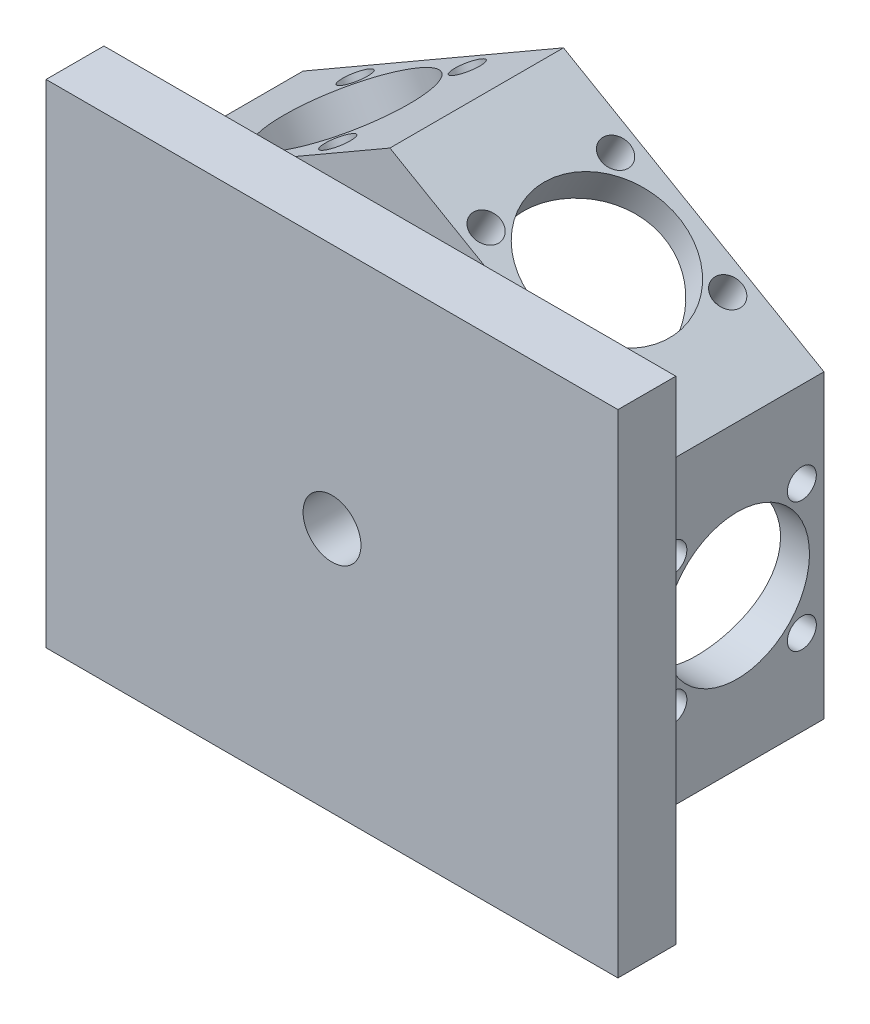
SolidWorks part; units mm, degrees
ref_plane "Front Plane" through (0, 0, 0) normal (0, 0, 1) x (1, 0, 0)
ref_plane "Top Plane" through (0, 0, 0) normal (0, 1, 0) x (1, 0, 0)
ref_plane "Right Plane" through (0, 0, 0) normal (1, 0, 0) x (0, 0, -1)
sketch "Sketch1" plane through (0, 0, 0) normal (0, 0, 1) x (1, 0, 0)
  line L1 (0, -51.9615) -> (45, -25.9808)
  line L2 (45, -25.9808) -> (45, 25.9808)
  line L3 (45, 25.9808) -> (0, 51.9615)
  line L4 (0, 51.9615) -> (-45, 25.9808)
  line L5 (-45, 25.9808) -> (-45, -25.9808)
  line L6 (-45, -25.9808) -> (0, -51.9615)
  circle A0 centre (0, 0) radius 45 construction
  circle A1 centre (0, 0) radius 40
  dimension "D2" = 5
  dimension "D1" = 90
extrude "Boss-Extrude1" add sketch "Sketch1" along normal blind 30
sketch "Sketch2" plane through (22.5, 38.9711, 0) normal (0.5, 0.866, 0) x (0.866, -0.5, 0)
  line L0 (0, 0) -> (0, -30) construction
  line L1 (25.9808, -30) -> (-25.9808, -30) construction
  line L3 (0, -15) -> (-11.1864, -3.8136) construction
  circle A0 centre (0, -15) radius 15.82 construction
  circle A1 centre (-11.1864, -3.8136) radius 2.5
  dimension "D1" = 31.64
  dimension "D2" = 5
extrude "Cut-Extrude1" cut sketch "Sketch2" against normal blind 30
sketch "Sketch3" plane through (22.5, 38.9711, 0) normal (0.5, 0.866, 0) x (0.866, -0.5, 0)
  line L0 (0, 0) -> (0, -30) construction
  line L1 (25.9808, -30) -> (-25.9808, -30) construction
  circle A0 centre (0, -15) radius 12.5
  dimension "D1" = 25
extrude "Cut-Extrude2" cut sketch "Sketch3" against normal blind 10
pattern_circular "CirPattern1" count 4 over 360 about axis through (0, 0, 15) along (0.5, 0.866, 0) of "Cut-Extrude1"
pattern_circular "CirPattern2" count 6 over 360 about axis through (0, 0, 30) along (0, 0, 1) of "CirPattern1", "Cut-Extrude2", "Cut-Extrude1"
sketch "Sketch4" plane through (0, 0, 30) normal (0, 0, 1) x (1, 0, 0)
  line L1 (-49.4075, 42.5271) -> (49.4075, 42.5271)
  line L2 (-49.4075, 42.5271) -> (-49.4075, -42.5271)
  line L3 (-49.4075, -42.5271) -> (49.4075, -42.5271)
  line L4 (49.4075, 42.5271) -> (49.4075, -42.5271)
  line L5 (-49.4075, 42.5271) -> (49.4075, -42.5271) construction
  line L6 (-49.4075, -42.5271) -> (49.4075, 42.5271) construction
  circle A0 centre (0, 0) radius 5
  point P0 (0, 0)
  dimension "D1" = 10
extrude "Boss-Extrude2" add sketch "Sketch4" along normal blind 10
